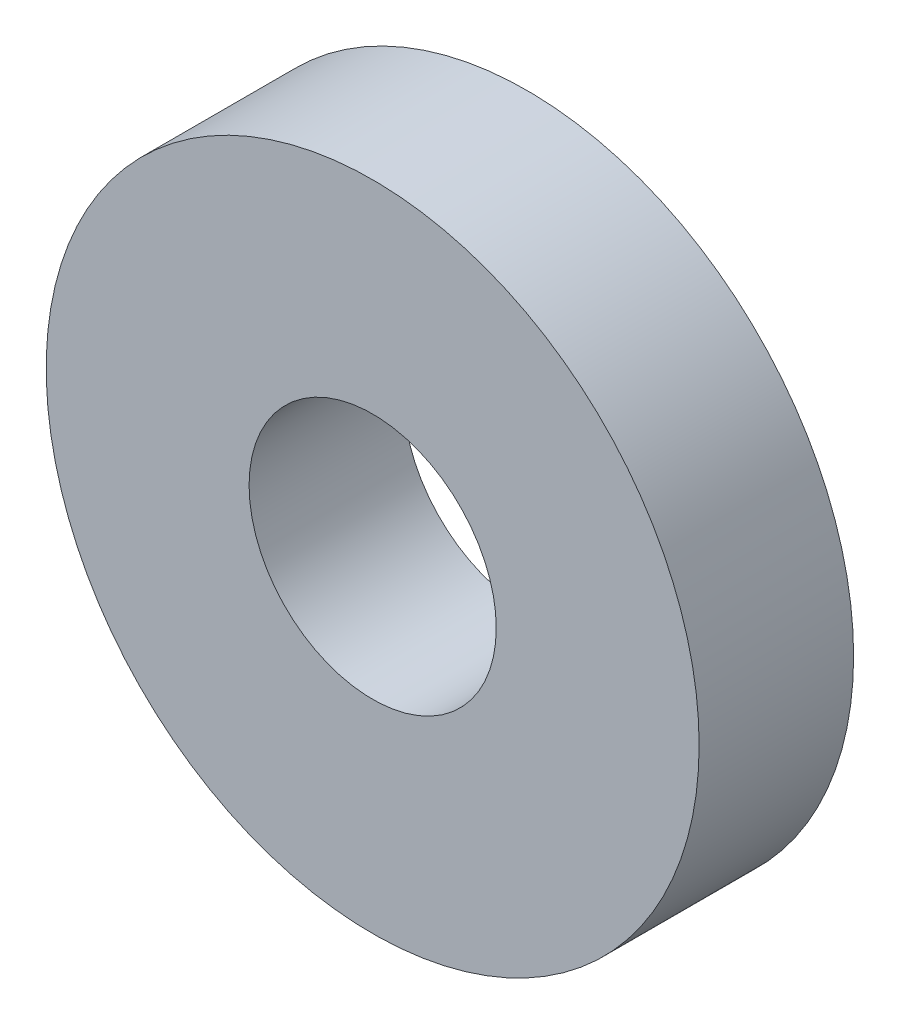
SolidWorks part; units mm, degrees
material "Силиконовая резина"
ref_plane "Спереди" through (0, 0, 0) normal (0, 0, 1) x (1, 0, 0)
ref_plane "Сверху" through (0, 0, 0) normal (0, 1, 0) x (1, 0, 0)
ref_plane "Справа" through (0, 0, 0) normal (1, 0, 0) x (0, 0, -1)
sketch "Эскиз1" plane through (0, 0, 0) normal (0, 0, 1) x (1, 0, 0)
  circle A0 centre (0, 0) radius 60
  circle A1 centre (0, 0) radius 158.5
  dimension "D1" = 120
  dimension "D2" = 317
extrude "Бобышка-Вытянуть1" add sketch "Эскиз1" along normal blind 75
